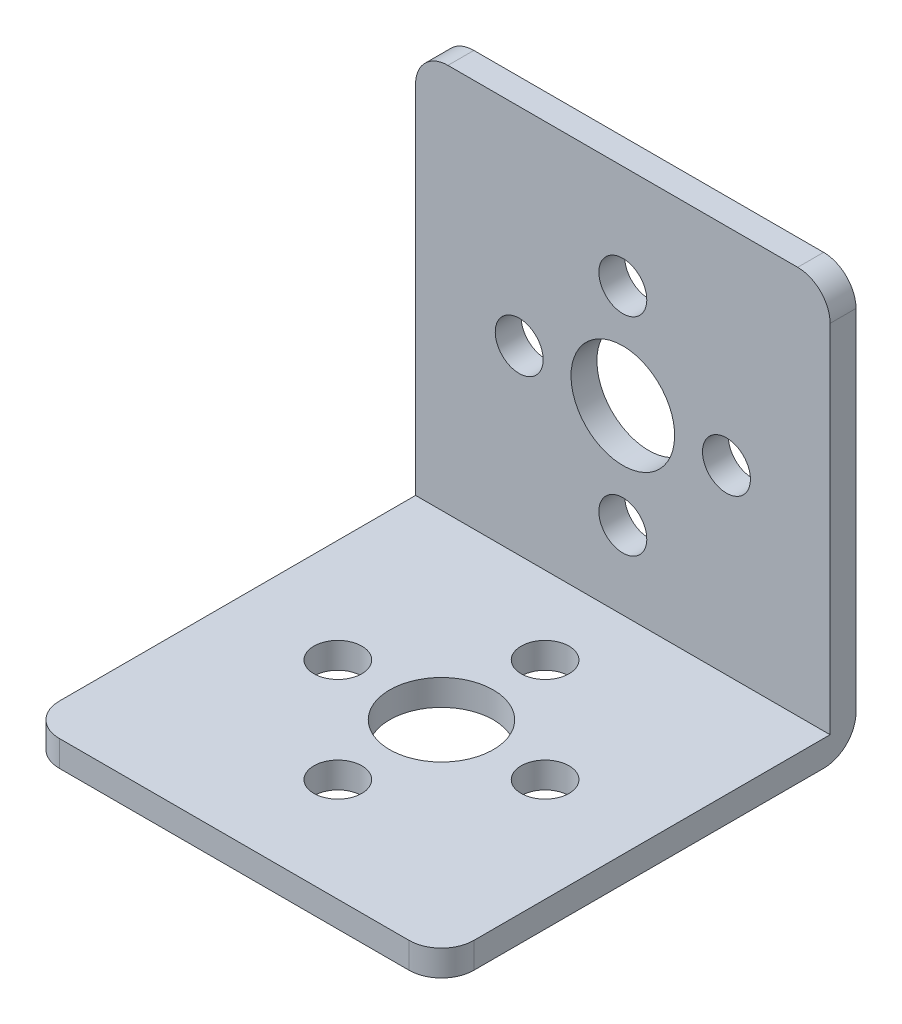
SolidWorks part; units mm, degrees
ref_plane "Front Plane" through (0, 0, 0) normal (0, 0, 1) x (1, 0, 0)
ref_plane "Top Plane" through (0, 0, 0) normal (0, 1, 0) x (1, 0, 0)
ref_plane "Right Plane" through (0, 0, 0) normal (1, 0, 0) x (0, 0, -1)
sketch "Sketch1" plane through (0, 0, 0) normal (1, 0, 0) x (0, 0, -1)
  line L1 (-16, 16) -> (16, 16)
  line L2 (-16, 16) -> (-16, -16)
  line L3 (-16, -16) -> (16, -16)
  line L4 (16, 16) -> (16, -16)
  line L5 (-16, 16) -> (16, -16) construction
  line L6 (-16, -16) -> (16, 16) construction
  point P0 (0, 0)
  dimension "D1" = 32
  dimension "D2" = 32
extrude "Boss-Extrude1" add sketch "Sketch1" along normal mid plane 32
sketch "Sketch2" plane through (16, 0, 0) normal (1, 0, 0) x (0, 0, -1)
  line L1 (-16, 16) -> (14, 16)
  line L2 (-16, 16) -> (-16, -14)
  line L3 (-16, -14) -> (14, -14)
  line L4 (14, 16) -> (14, -14)
  dimension "D1" = 30
  dimension "D2" = 30
extrude "Cut-Extrude1" cut sketch "Sketch2" against normal blind 32
sketch "Sketch3" plane through (0, 0, -16) normal (0, 0, -1) x (-1, 0, 0)
  circle A0 centre (0, 0) radius 4
  circle A1 centre (8, 0) radius 1.85
  circle A2 centre (-8, 0) radius 1.85
  circle A3 centre (0, 8) radius 1.85
  circle A4 centre (0, -8) radius 1.85
  dimension "D1" = 8
  dimension "D2" = 8
  dimension "D3" = 8
  dimension "D4" = 8
extrude "Cut-Extrude2" cut sketch "Sketch3" against normal through all
sketch "Sketch4" plane through (0, -16, 0) normal (0, -1, 0) x (1, 0, 0)
  circle A0 centre (0, 0) radius 4
  circle A1 centre (8, 0) radius 1.85
  circle A2 centre (-8, 0) radius 1.85
  circle A3 centre (0, 8) radius 1.85
  circle A4 centre (0, -8) radius 1.85
  dimension "D1" = 8
  dimension "D2" = 8
  dimension "D3" = 8
  dimension "D4" = 8
extrude "Cut-Extrude3" cut sketch "Sketch4" against normal through all
fillet "Fillet1" radius 2.5 5 edges at (0, -16, -16) (-16, -15, 16) (16, -15, 16) (-16, 16, -15) (16, 16, -15)
